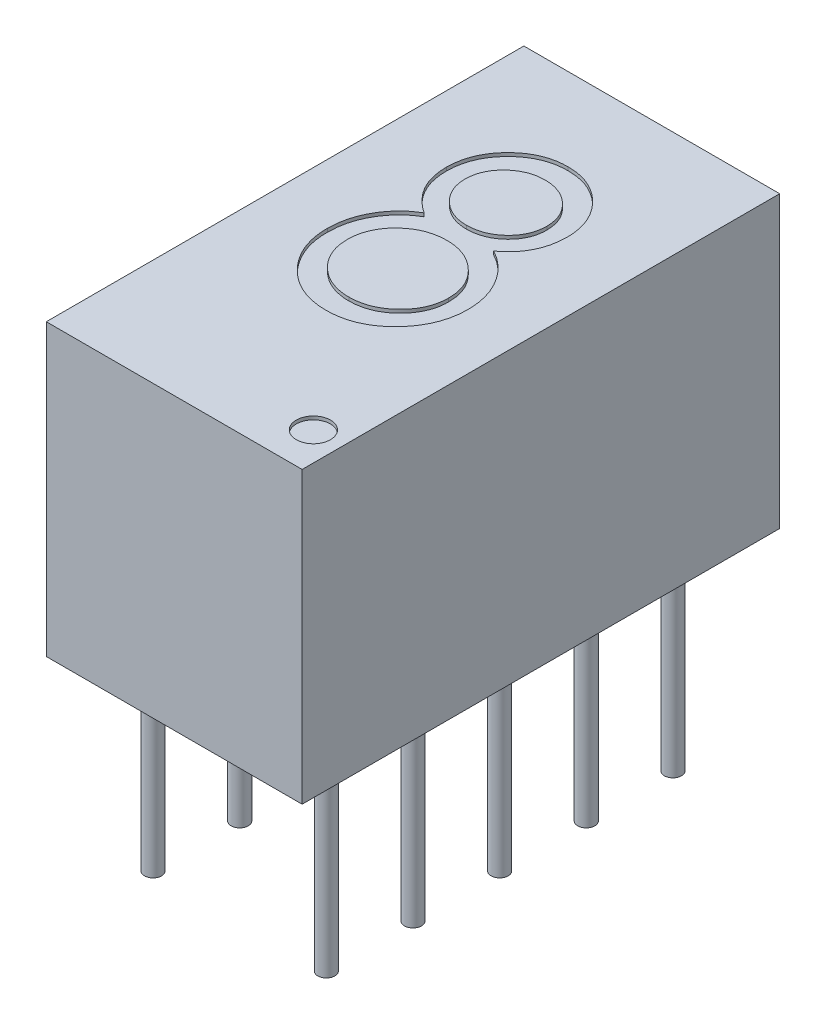
SolidWorks part; units mm, degrees
ref_plane "Спереди" through (0, 0, 0) normal (0, 0, 1) x (1, 0, 0)
ref_plane "Сверху" through (0, 0, 0) normal (0, 1, 0) x (1, 0, 0)
ref_plane "Справа" through (0, 0, 0) normal (1, 0, 0) x (0, 0, -1)
sketch "Эскиз1" plane through (0, 0, 0) normal (0, 1, 0) x (1, 0, 0)
  line L1 (-3.75, 7) -> (3.75, 7)
  line L2 (-3.75, 7) -> (-3.75, -7)
  line L3 (-3.75, -7) -> (3.75, -7)
  line L4 (3.75, 7) -> (3.75, -7)
  line L5 (-3.75, 7) -> (3.75, -7) construction
  line L6 (-3.75, -7) -> (3.75, 7) construction
  point P0 (0, 0)
  dimension "D1" = 7.5
  dimension "D2" = 14
extrude "Бобышка-Вытянуть1" add sketch "Эскиз1" along normal blind 8.5
sketch "Эскиз3" plane through (0, 8.5, 0) normal (0, 1, 0) x (1, 0, 0)
  circle A0 centre (2.9105, -5.8309) radius 0.5
  text T0 "8" font "Technic" height in points 28
  point P15 (0, 0)
  dimension "D4" = 1
extrude "Вырез-Вытянуть1" cut sketch "Эскиз3" against normal blind 0.1
sketch "Эскиз4" plane through (0, 0, 0) normal (0, -1, 0) x (1, 0, 0)
  line L0 (0, -7.7556) -> (0, 9.2995) construction
  line L1 (5.8306, 0) -> (-5.5801, 0) construction
sketch "Эскиз5" plane through (0, 0, 0) normal (0, -1, 0) x (1, 0, 0)
  line L0 (5.8306, 0) -> (-5.5801, 0) construction
  line L1 (0, -7.7556) -> (0, 9.2995) construction
  circle A0 centre (-2.54, -5.08) radius 0.25
  circle A1 centre (2.54, -5.08) radius 0.25
  circle A2 centre (2.54, -2.54) radius 0.25
  circle A3 centre (2.54, 0) radius 0.25
  circle A4 centre (2.54, 2.54) radius 0.25
  circle A5 centre (2.54, 5.08) radius 0.25
  circle A6 centre (-2.54, -2.54) radius 0.25
  circle A7 centre (-2.54, 0) radius 0.25
  circle A8 centre (-2.54, 2.54) radius 0.25
  circle A9 centre (-2.54, 5.08) radius 0.25
  dimension "D1" = 0.5
  dimension "D4" = 5.08
  dimension "D5" = 2.54
  dimension "D2" = 2
  dimension "D3" = 5
extrude "Бобышка-Вытянуть2" add sketch "Эскиз5" along normal blind 5.8
